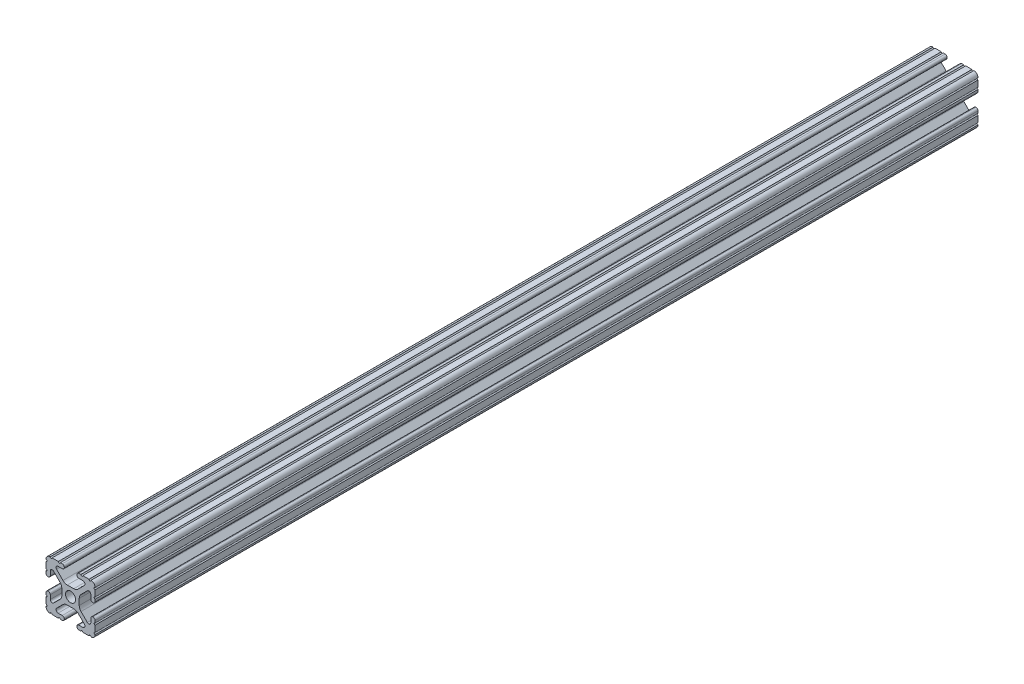
SolidWorks part; units mm, degrees
material "6061 Alloy"
ref_plane "Front Plane" through (0, 0, 0) normal (0, 0, 1) x (1, 0, 0)
ref_plane "Top Plane" through (0, 0, 0) normal (0, 1, 0) x (1, 0, 0)
ref_plane "Right Plane" through (0, 0, 0) normal (1, 0, 0) x (0, 0, -1)
sketch "Sketch1" plane through (0, 0, 0) normal (0, 0, 1) x (1, 0, 0)
  line L0 (-7.2072, 8.7245) -> (-3.9003, 5.4237)
  line L1 (-4.2875, 10.4902) -> (-6.4768, 10.4902)
  line L2 (-3.2384, 11.651) -> (-3.2384, 11.5392)
  line L3 (-5.3171, 12.7) -> (-4.2875, 12.7)
  line L4 (0, 13.4005) -> (0, -14.8534) construction
  line L5 (12.7, 0) -> (-13.9989, 0) construction
  line L6 (-9.5504, 12.7) -> (-6.3331, 12.7)
  line L7 (-12.7, 6.3331) -> (-12.7, 9.5504)
  line L8 (-12.7, 4.2875) -> (-12.7, 5.3171)
  line L9 (-11.5392, 3.2385) -> (-11.651, 3.2385)
  line L10 (-10.4902, 6.4021) -> (-10.4902, 4.2875)
  line L11 (-5.4405, 3.8388) -> (-8.737, 7.1292)
  line L12 (-4.5085, -1.5917) -> (-4.5085, 1.5917)
  line L13 (-1.7093, -4.4958) -> (1.7093, -4.4958)
  line L14 (3.9523, -5.4237) -> (7.1797, -8.6452)
  line L15 (6.4164, -10.4902) -> (4.2875, -10.4902)
  line L16 (3.2385, -11.5392) -> (3.2385, -11.651)
  line L17 (4.2875, -12.7) -> (5.3171, -12.7)
  line L18 (6.3331, -12.7) -> (9.5504, -12.7)
  line L19 (12.7, -9.5504) -> (12.7, -6.3331)
  line L20 (12.7, -5.3171) -> (12.7, -4.2875)
  line L21 (11.651, -3.2385) -> (11.5392, -3.2385)
  line L22 (10.4902, -4.2875) -> (10.4902, -6.4021)
  line L23 (8.737, -7.1292) -> (5.4405, -3.8388)
  line L24 (4.5085, -1.5917) -> (4.5085, 1.5917)
  line L25 (5.4405, 3.8388) -> (8.737, 7.1292)
  line L26 (10.4902, 6.4021) -> (10.4902, 4.2875)
  line L27 (11.5392, 3.2385) -> (11.651, 3.2385)
  line L28 (12.7, 4.2875) -> (12.7, 5.3171)
  line L29 (12.7, 6.3331) -> (12.7, 9.5504)
  line L30 (9.5504, 12.7) -> (6.3331, 12.7)
  line L31 (5.3171, 12.7) -> (4.2875, 12.7)
  line L32 (3.2384, 11.651) -> (3.2384, 11.5392)
  line L33 (4.2875, 10.4902) -> (6.4768, 10.4902)
  line L34 (7.2072, 8.7245) -> (3.9003, 5.4237)
  line L35 (1.6573, 4.4958) -> (-1.6573, 4.4958)
  line L36 (-8.737, -7.1292) -> (-5.4405, -3.8388)
  line L37 (-10.4902, -4.2875) -> (-10.4902, -6.4021)
  line L38 (-11.651, -3.2385) -> (-11.5392, -3.2385)
  line L39 (-12.7, -5.3171) -> (-12.7, -4.2875)
  line L40 (-12.7, -9.5504) -> (-12.7, -6.3331)
  line L41 (-6.3331, -12.7) -> (-9.5504, -12.7)
  line L42 (-4.2875, -12.7) -> (-5.3171, -12.7)
  line L43 (-3.2385, -11.5392) -> (-3.2385, -11.651)
  line L44 (-6.4164, -10.4902) -> (-4.2875, -10.4902)
  line L45 (-3.9523, -5.4237) -> (-7.1797, -8.6452)
  arc A0 (-7.2072, 8.7245) -> (-6.4768, 10.4902) centre (-6.4768, 9.4563) cw
  arc A1 (-3.2384, 11.5392) -> (-4.2875, 10.4902) centre (-4.2875, 11.5392) cw
  arc A2 (-4.2875, 12.7) -> (-3.2384, 11.651) centre (-4.2875, 11.651) cw
  arc A3 (-5.3171, 12.7) -> (-6.3331, 12.7) centre (-5.8251, 12.7) cw
  arc A4 (-9.5504, 12.7) -> (-10.5664, 12.6998) centre (-10.0584, 12.7) cw
  arc A5 (-12.6998, 10.5664) -> (-10.5664, 12.6998) centre (-10.5918, 10.5918) cw
  arc A6 (-12.6998, 10.5664) -> (-12.7, 9.5504) centre (-12.7, 10.0584) cw
  arc A7 (-12.7, 6.3331) -> (-12.7, 5.3171) centre (-12.7, 5.8251) cw
  arc A8 (-11.651, 3.2385) -> (-12.7, 4.2875) centre (-11.651, 4.2875) cw
  arc A9 (-10.4902, 4.2875) -> (-11.5392, 3.2385) centre (-11.5392, 4.2875) cw
  circle A10 centre (0, 0) radius 2.6035
  arc A11 (-10.4902, 6.4021) -> (-8.737, 7.1292) centre (-9.4628, 6.4021) cw
  arc A12 (-5.4405, 3.8388) -> (-4.5085, 1.5917) centre (-7.6835, 1.5917) cw
  arc A13 (-4.5085, -1.5917) -> (-5.4405, -3.8388) centre (-7.6835, -1.5917) cw
  arc A14 (-8.737, -7.1292) -> (-10.4902, -6.4021) centre (-9.4628, -6.4021) cw
  arc A15 (-1.7093, -4.4958) -> (-3.9523, -5.4237) centre (-1.7093, -7.6708) ccw
  arc A16 (3.9523, -5.4237) -> (1.7093, -4.4958) centre (1.7093, -7.6708) ccw
  arc A17 (6.4164, -10.4902) -> (7.1797, -8.6452) centre (6.4164, -9.4098) ccw
  arc A18 (4.2875, -10.4902) -> (3.2385, -11.5392) centre (4.2875, -11.5392) ccw
  arc A19 (3.2385, -11.651) -> (4.2875, -12.7) centre (4.2875, -11.651) ccw
  arc A20 (6.3331, -12.7) -> (5.3171, -12.7) centre (5.8251, -12.7) ccw
  arc A21 (10.5664, -12.6998) -> (9.5504, -12.7) centre (10.0584, -12.7) ccw
  arc A22 (10.5664, -12.6998) -> (12.6998, -10.5664) centre (10.5918, -10.5918) ccw
  arc A23 (12.7, -9.5504) -> (12.6998, -10.5664) centre (12.7, -10.0584) ccw
  arc A24 (12.7, -5.3171) -> (12.7, -6.3331) centre (12.7, -5.8251) ccw
  arc A25 (12.7, -4.2875) -> (11.651, -3.2385) centre (11.651, -4.2875) ccw
  arc A26 (11.5392, -3.2385) -> (10.4902, -4.2875) centre (11.5392, -4.2875) ccw
  arc A27 (8.737, -7.1292) -> (10.4902, -6.4021) centre (9.4628, -6.4021) ccw
  arc A28 (4.5085, -1.5917) -> (5.4405, -3.8388) centre (7.6835, -1.5917) ccw
  arc A29 (5.4405, 3.8388) -> (4.5085, 1.5917) centre (7.6835, 1.5917) ccw
  arc A30 (10.4902, 6.4021) -> (8.737, 7.1292) centre (9.4628, 6.4021) ccw
  arc A31 (10.4902, 4.2875) -> (11.5392, 3.2385) centre (11.5392, 4.2875) ccw
  arc A32 (11.651, 3.2385) -> (12.7, 4.2875) centre (11.651, 4.2875) ccw
  arc A33 (12.7, 6.3331) -> (12.7, 5.3171) centre (12.7, 5.8251) ccw
  arc A34 (12.6998, 10.5664) -> (12.7, 9.5504) centre (12.7, 10.0584) ccw
  arc A35 (12.6998, 10.5664) -> (10.5664, 12.6998) centre (10.5918, 10.5918) ccw
  arc A36 (9.5504, 12.7) -> (10.5664, 12.6998) centre (10.0584, 12.7) ccw
  arc A37 (5.3171, 12.7) -> (6.3331, 12.7) centre (5.8251, 12.7) ccw
  arc A38 (4.2875, 12.7) -> (3.2384, 11.651) centre (4.2875, 11.651) ccw
  arc A39 (3.2384, 11.5392) -> (4.2875, 10.4902) centre (4.2875, 11.5392) ccw
  arc A40 (7.2072, 8.7245) -> (6.4768, 10.4902) centre (6.4768, 9.4563) ccw
  arc A41 (1.6573, 4.4958) -> (3.9003, 5.4237) centre (1.6573, 7.6708) ccw
  arc A42 (-1.6573, 4.4958) -> (-3.9003, 5.4237) centre (-1.6573, 7.6708) cw
  arc A43 (-11.5392, -3.2385) -> (-10.4902, -4.2875) centre (-11.5392, -4.2875) cw
  arc A44 (-12.7, -4.2875) -> (-11.651, -3.2385) centre (-11.651, -4.2875) cw
  arc A45 (-12.7, -5.3171) -> (-12.7, -6.3331) centre (-12.7, -5.8251) cw
  arc A46 (-12.7, -9.5504) -> (-12.6998, -10.5664) centre (-12.7, -10.0584) cw
  arc A47 (-10.5664, -12.6998) -> (-12.6998, -10.5664) centre (-10.5918, -10.5918) cw
  arc A48 (-10.5664, -12.6998) -> (-9.5504, -12.7) centre (-10.0584, -12.7) cw
  arc A49 (-6.3331, -12.7) -> (-5.3171, -12.7) centre (-5.8251, -12.7) cw
  arc A50 (-3.2385, -11.651) -> (-4.2875, -12.7) centre (-4.2875, -11.651) cw
  arc A51 (-4.2875, -10.4902) -> (-3.2385, -11.5392) centre (-4.2875, -11.5392) cw
  arc A52 (-6.4164, -10.4902) -> (-7.1797, -8.6452) centre (-6.4164, -9.4098) cw
  dimension "D1" = 5.207
  dimension "D9" = 14.859
  dimension "D2" = 25.4
  dimension "D3" = 12.7
  dimension "D4" = 6.477
  dimension "D5" = 8.2042
  dimension "D6" = 9.017
  dimension "D8" = 2.2098
  dimension "D10" = 2.2098
extrude "Extrude1" add sketch "Sketch1" against normal blind 457.2
